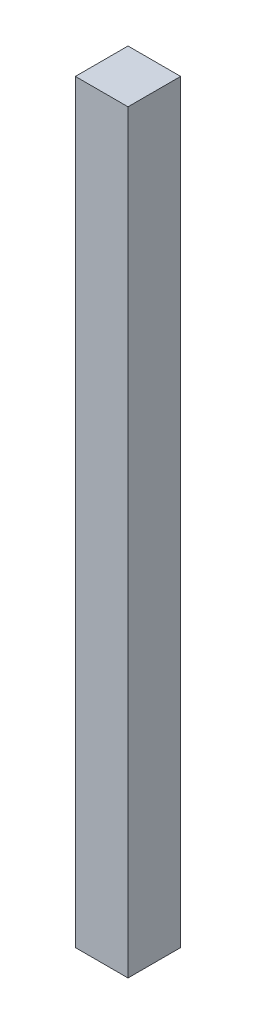
SolidWorks part; units mm, degrees
ref_plane "Front Plane" through (0, 0, 0) normal (0, 0, 1) x (1, 0, 0)
ref_plane "Top Plane" through (0, 0, 0) normal (0, 1, 0) x (1, 0, 0)
ref_plane "Right Plane" through (0, 0, 0) normal (1, 0, 0) x (0, 0, -1)
sketch "Sketch1" plane through (0, 0, 0) normal (0, 1, 0) x (1, 0, 0)
  line L1 (0, 0) -> (6, 0)
  line L2 (0, 0) -> (0, -6)
  line L3 (0, -6) -> (6, -6)
  line L4 (6, 0) -> (6, -6)
  dimension "D1" = 6
  dimension "D2" = 6
extrude "Boss-Extrude1" add sketch "Sketch1" along normal blind 86
